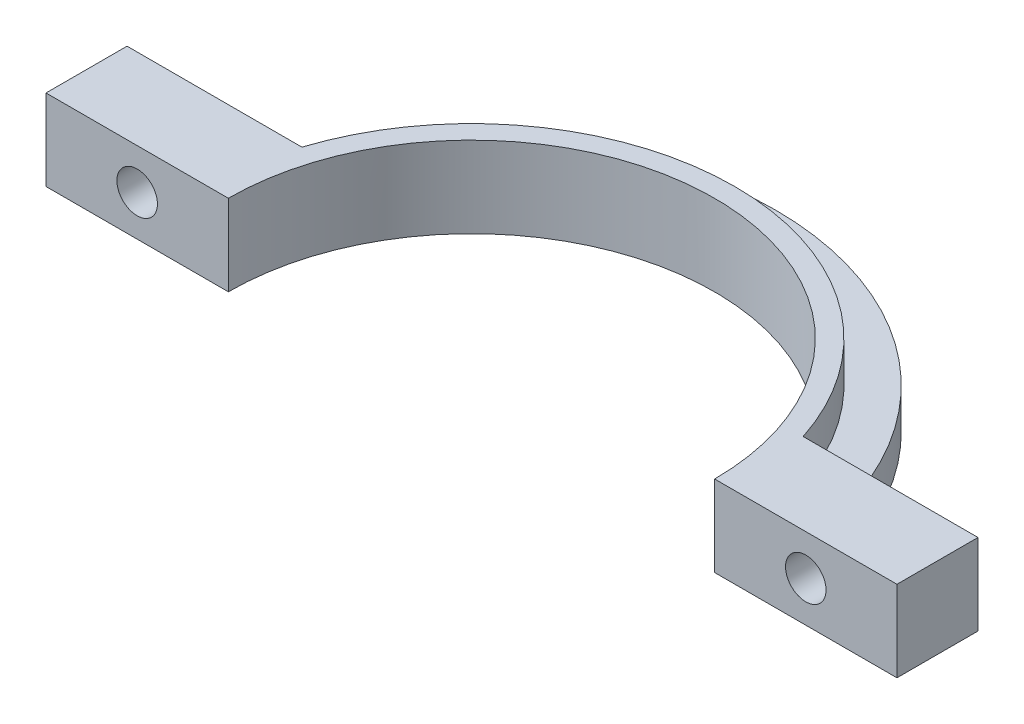
SolidWorks part; units mm, degrees
ref_plane "Front Plane" through (0, 0, 0) normal (0, 0, 1) x (1, 0, 0)
ref_plane "Top Plane" through (0, 0, 0) normal (0, 1, 0) x (1, 0, 0)
ref_plane "Right Plane" through (0, 0, 0) normal (1, 0, 0) x (0, 0, -1)
sketch "Sketch1" plane through (0, 0, 0) normal (0, 1, 0) x (1, 0, 0)
  line L2 (0, 30) -> (0, -30) construction
  line L3 (32.5, 0) -> (52.5, 0)
  line L4 (52.5, 0) -> (52.5, 10)
  line L5 (-32.5, 0) -> (-52.5, 0)
  line L6 (-52.5, 0) -> (-52.5, 10)
  line L7 (52.5, 10) -> (30.9233, 10)
  line L8 (-41.7116, 10) -> (-41.7116, 15) construction
  line L9 (-28.8314, 15) -> (-78.8314, 15)
  line L11 (-30, 0) -> (-32.5, 0)
  line L12 (30, 0) -> (32.5, 0)
  line L13 (-52.5, 10) -> (-30.9233, 10)
  circle A0 centre (0, 0) radius 30
  circle A3 centre (0, 0) radius 32.5
  point P8 (0, 47.5)
  dimension "D1" = 60
  dimension "D2" = 65
  dimension "D4" = 50
  dimension "D3" = 5
  dimension "D5" = 20
  dimension "D6" = 10
extrude "Boss-Extrude1" add sketch "Sketch1" along normal blind 10
sketch "Sketch3" plane through (0, 0, 0) normal (0, 0, 1) x (1, 0, 0)
  line L0 (-52.5, 5) -> (-30, 5) construction
  line L3 (-52.5, 10) -> (-52.5, 0) construction
  line L6 (-30, 10) -> (-30, 0) construction
  line L7 (30, 5) -> (52.5, 5) construction
  line L8 (30, 10) -> (30, 0) construction
  line L9 (52.5, 10) -> (52.5, 0) construction
  circle A2 centre (-41.25, 5) radius 2.5
  circle A3 centre (41.25, 5) radius 2.5
  dimension "D1" = 5
extrude "Cut-Extrude1" cut sketch "Sketch3" against normal blind 10
sketch "Sketch5" plane through (0, 0, 0) normal (0, 1, 0) x (1, 0, 0)
  line L0 (-37.5, 0) -> (-32.5, 0)
  line L1 (32.5, 0) -> (37.5, 0)
  circle A0 centre (0, 0) radius 37.5
  circle A1 centre (0, 0) radius 32.5
  dimension "D1" = 75
  dimension "D2" = 65
extrude "Boss-Extrude2" add sketch "Sketch5" along normal blind 5 contours A1 L1 A0 L0
sketch "Sketch9" plane through (0, 0, 0) normal (0, -1, 0) x (1, 0, 0)
  line L0 (-34.8065, -10) -> (-28.2843, -10)
  line L1 (-34.8065, -13.9556) -> (-28.2843, -13.9556)
  line L2 (0, 0) -> (0, -30) construction
  line L5 (-34.8065, -13.9556) -> (-34.8065, -10)
  line L6 (-28.2843, -10) -> (-28.2843, -13.9556)
  line L7 (34.8065, -13.9556) -> (28.2843, -13.9556)
  line L8 (34.8065, -13.9556) -> (34.8065, -10)
  line L9 (34.8065, -10) -> (28.2843, -10)
  line L10 (28.2843, -10) -> (28.2843, -13.9556)
  arc A0 (-30, 0) -> (30, 0) centre (0, 0) ccw construction
  arc A1 (-36.1421, -10) -> (36.1421, -10) centre (0, 0) ccw construction
  dimension "D2" = 3.9556
  dimension "D1" = 6.5222
extrude "Boss-Extrude3" add sketch "Sketch9" along normal blind 10 contours L9 L10 L7 L8
chamfer "Chamfer1" distance 1 angle 45 2 edges at (28.2843, -10, -11.9778) (34.8065, -10, -11.9778)
sketch "Sketch12" plane through (0, 0, -13.9556) normal (0, 0, -1) x (-1, 0, 0)
  line L0 (-31.5454, -10) -> (-31.5454, -6) construction
  line L1 (-33.8065, -10) -> (-29.2843, -10) construction
  circle A0 centre (-31.5454, -6) radius 2
  dimension "D2" = 4
  dimension "D1" = 4
extrude "Cut-Extrude4" cut sketch "Sketch12" against normal blind 10
